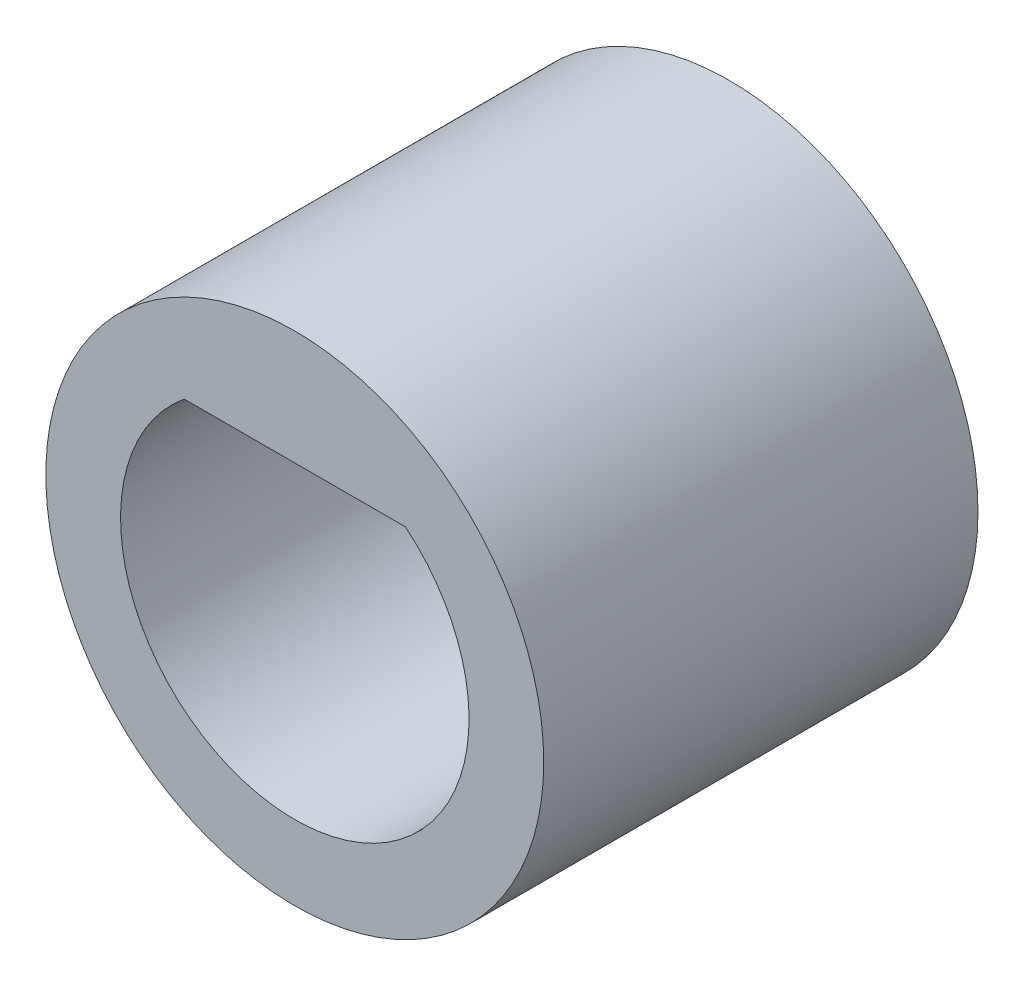
SolidWorks part; units mm, degrees
ref_plane "Front Plane" through (0, 0, 0) normal (0, 0, 1) x (1, 0, 0)
ref_plane "Top Plane" through (0, 0, 0) normal (0, 1, 0) x (1, 0, 0)
ref_plane "Right Plane" through (0, 0, 0) normal (1, 0, 0) x (0, 0, -1)
sketch "Sketch1" plane through (0, 0, 0) normal (0, 0, 1) x (1, 0, 0)
  circle A0 centre (0, 0) radius 5.715
  dimension "D1" = 11.43
extrude "Boss-Extrude1" add sketch "Sketch1" along normal blind 9.969
sketch "Sketch2" plane through (0, 0, 0) normal (0, 0, -1) x (-1, 0, 0)
  circle A0 centre (0, 0) radius 2.3876
  dimension "D1" = 4.7752
extrude "Cut-Extrude1" cut sketch "Sketch2" against normal through all
sketch "Sketch3" plane through (0, 0, 9.969) normal (0, 0, 1) x (1, 0, 0)
  circle A0 centre (0, 0) radius 4
  circle A1 centre (0, 0) radius 5.715 construction
  dimension "D1" = 8
extrude "Cut-Extrude2" cut sketch "Sketch3" against normal blind 6.35
sketch "Sketch4" plane through (0, 0, 9.969) normal (0, 0, 1) x (1, 0, 0)
  line L0 (2.54, 3.09) -> (-2.54, 3.09)
  circle A0 centre (0, 0) radius 4 construction
  circle A1 centre (0, 0) radius 4 construction
  arc A2 (2.54, 3.09) -> (-2.54, 3.09) centre (0, 0) ccw
  dimension "D1" = 5.08
extrude "Boss-Extrude2" add sketch "Sketch4" against normal up to surface (6.35 mm away) up to face at (4, 0, 3.619)
